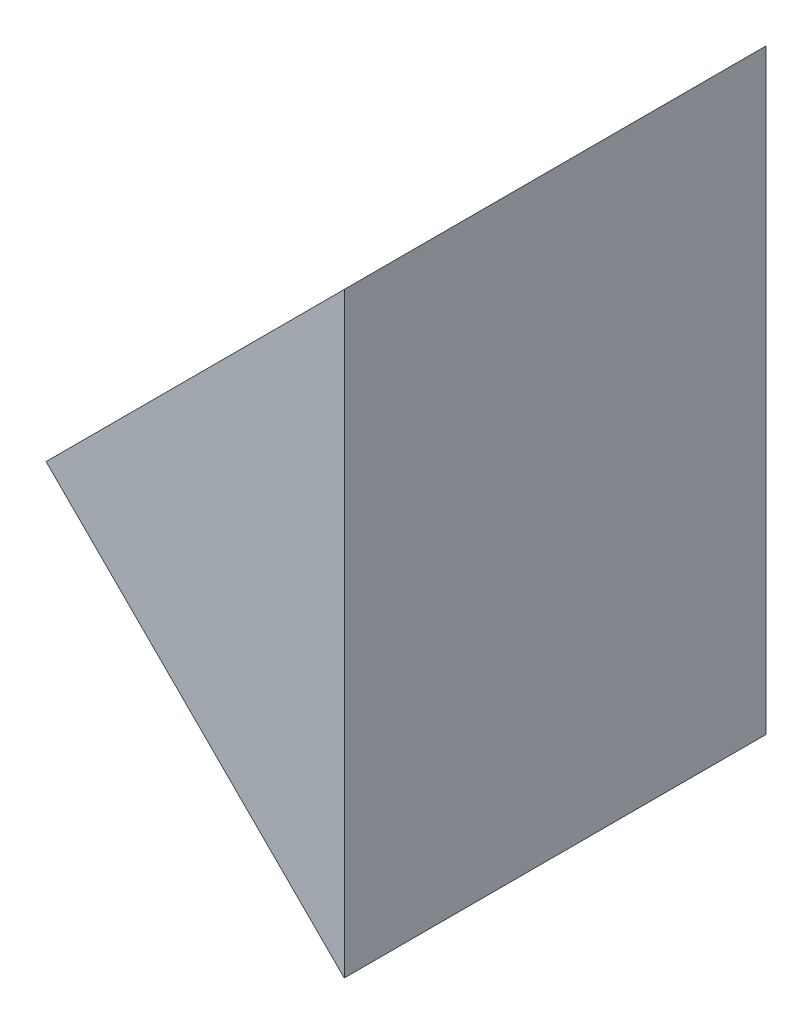
SolidWorks part; units mm, degrees
ref_plane "前视基准面" through (0, 0, 0) normal (0, 0, 1) x (1, 0, 0)
ref_plane "上视基准面" through (0, 0, 0) normal (0, 1, 0) x (1, 0, 0)
ref_plane "右视基准面" through (0, 0, 0) normal (1, 0, 0) x (0, 0, -1)
sketch "草图1" plane through (0, 0, 0) normal (0, 0, 1) x (1, 0, 0)
  line L0 (295.061, 90.0917) -> (273.8478, 68.8785)
  line L1 (273.8478, 68.8785) -> (295.061, 47.6653)
  line L2 (295.061, 47.6653) -> (295.061, 90.0917)
  dimension "D1" = 30
  dimension "D2" = 30
extrude "凸台-拉伸1" add sketch "草图1" along normal blind 30
